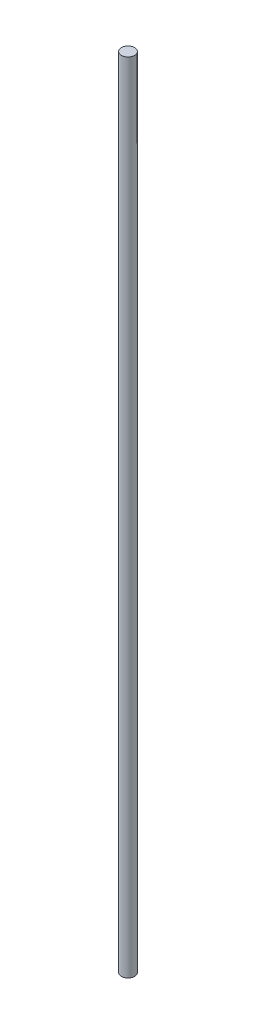
SolidWorks part; units mm, degrees
material "Alloy Steel"
ref_plane "Front Plane" through (0, 0, 0) normal (0, 0, 1) x (1, 0, 0)
ref_plane "Top Plane" through (0, 0, 0) normal (0, 1, 0) x (1, 0, 0)
ref_plane "Right Plane" through (0, 0, 0) normal (1, 0, 0) x (0, 0, -1)
sketch "Sketch1" plane through (0, 0, 0) normal (0, 1, 0) x (1, 0, 0)
  circle A0 centre (0, 0) radius 4
  dimension "D1" = 8
extrude "Boss-Extrude1" add sketch "Sketch1" along normal blind 475
